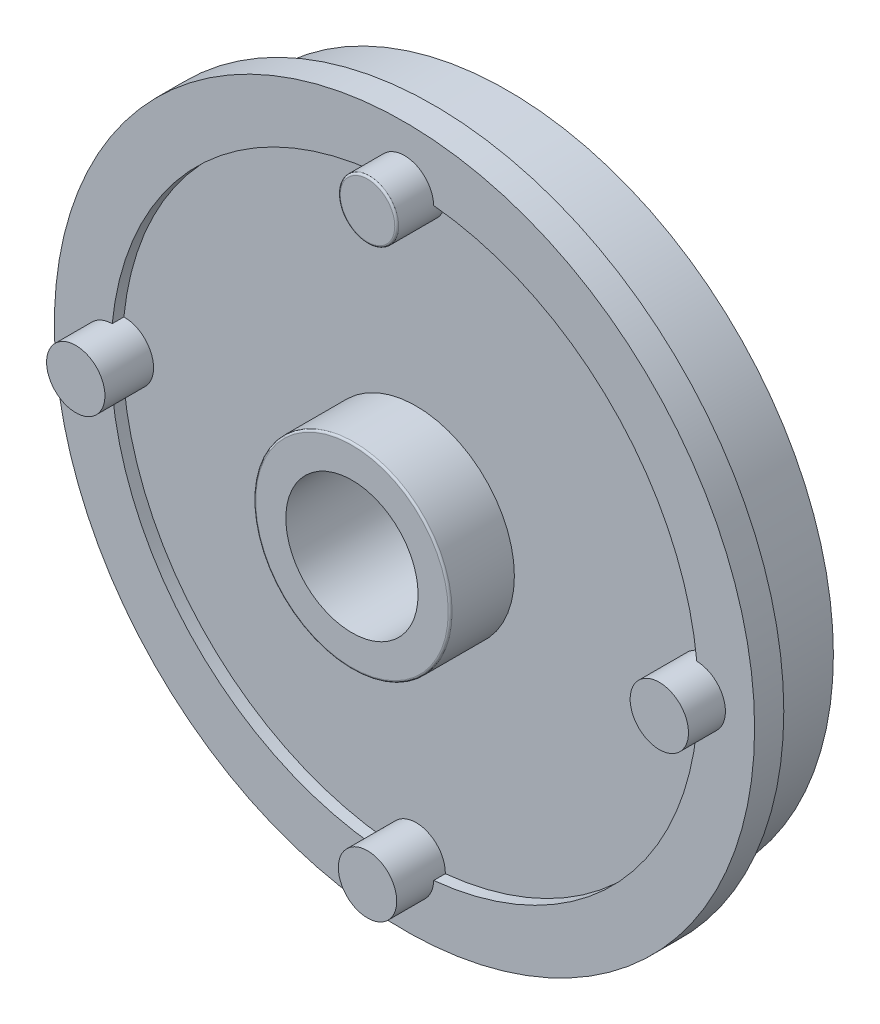
SolidWorks part; units mm, degrees
material "ABS"
ref_plane "Front Plane" through (0, 0, 0) normal (0, 0, 1) x (1, 0, 0)
ref_plane "Top Plane" through (0, 0, 0) normal (0, 1, 0) x (1, 0, 0)
ref_plane "Right Plane" through (0, 0, 0) normal (1, 0, 0) x (0, 0, -1)
sketch "Sketch1" plane through (0, 0, 0) normal (0, 0, 1) x (1, 0, 0)
  circle A2 centre (0, 0) radius 16.75
  dimension "D3" = 33.5
extrude "Boss-Extrude1" add sketch "Sketch1" along normal blind 3.8
sketch "Sketch2" plane through (0, 0, 3.8) normal (0, 0, 1) x (1, 0, 0)
  circle A0 centre (0, 0) radius 18
  dimension "D1" = 36
extrude "Boss-Extrude2" add sketch "Sketch2" along normal blind 1.5
sketch "Sketch3" plane through (0, 0, 0) normal (0, 0, -1) x (-1, 0, 0)
  circle A0 centre (0, 0) radius 13.25
  dimension "D1" = 26.5
extrude "Cut-Extrude1" cut sketch "Sketch3" against normal blind 4
sketch "Sketch4" plane through (0, 0, 4) normal (0, 0, -1) x (-1, 0, 0)
  circle A0 centre (0, 0) radius 5
  dimension "D1" = 10
extrude "Boss-Extrude3" add sketch "Sketch4" along normal blind 6.5
sketch "Sketch5" plane through (0, 0, -2.5) normal (0, 0, -1) x (-1, 0, 0)
  circle A0 centre (0, 0) radius 4
  dimension "D1" = 8
extrude "Cut-Extrude2" cut sketch "Sketch5" against normal blind 2
sketch "Sketch7" plane through (0, 0, 5.3) normal (0, 0, 1) x (1, 0, 0)
  circle A0 centre (0, 0) radius 15.1
  dimension "D1" = 30.2
extrude "Cut-Extrude3" cut sketch "Sketch7" against normal blind 0.6
sketch "Sketch8" plane through (0, 0, 4.7) normal (0, 0, 1) x (1, 0, 0)
  circle A0 centre (0, 0) radius 5.05
  dimension "D1" = 10.1
extrude "Boss-Extrude4" add sketch "Sketch8" along normal blind 3.3
sketch "Sketch6" plane through (0, 0, -0.5) normal (0, 0, -1) x (-1, 0, 0)
  circle A0 centre (0, 0) radius 2.65
  dimension "D1" = 5.3
extrude "Cut-Extrude4" cut sketch "Sketch6" against normal through all
sketch "Sketch9" plane through (0, 0, 8) normal (0, 0, 1) x (1, 0, 0)
  circle A0 centre (0, 0) radius 3.4
  dimension "D1" = 6.8
extrude "Cut-Extrude5" cut sketch "Sketch9" against normal blind 7
sketch "Sketch10" plane through (0, 0, 4.7) normal (0, 0, 1) x (1, 0, 0)
  line L0 (0, -5.775) -> (0, 5.775) construction
  line L1 (5.775, 0) -> (-5.775, 0) construction
  circle A0 centre (0, 15) radius 1.5
  dimension "D1" = 3
  dimension "D2" = 0
  dimension "D3" = 15
extrude "Boss-Extrude5" add sketch "Sketch10" along normal blind 2.5
fillet "Fillet2" radius 0.1 1 edges at (1.5, 15, 7.2)
fillet "Fillet3" radius 0.1 1 edges at (5.05, 0, 8)
pattern_circular "CirPattern1" count 4 over 360 about axis through (0, 0, 0) along (0, 0, 1) of "Boss-Extrude5"
